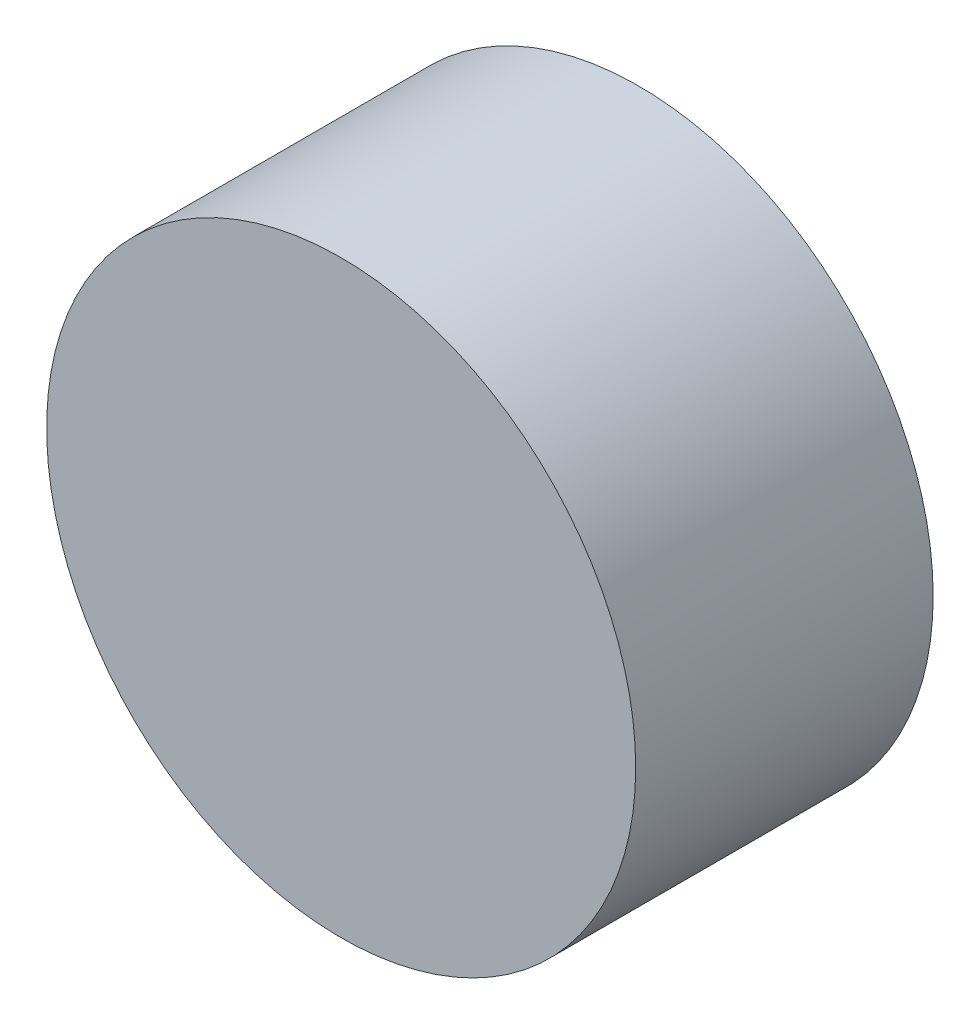
SolidWorks part; units mm, degrees
ref_plane "Front Plane" through (0, 0, 0) normal (0, 0, 1) x (1, 0, 0)
ref_plane "Top Plane" through (0, 0, 0) normal (0, 1, 0) x (1, 0, 0)
ref_plane "Right Plane" through (0, 0, 0) normal (1, 0, 0) x (0, 0, -1)
sketch "Sketch1" plane through (0, 0, 0) normal (0, 0, 1) x (1, 0, 0)
  circle A0 centre (0, 0) radius 1.505
  dimension "D1" = 3.01
extrude "Boss-Extrude1" add sketch "Sketch1" along normal blind 1.52
